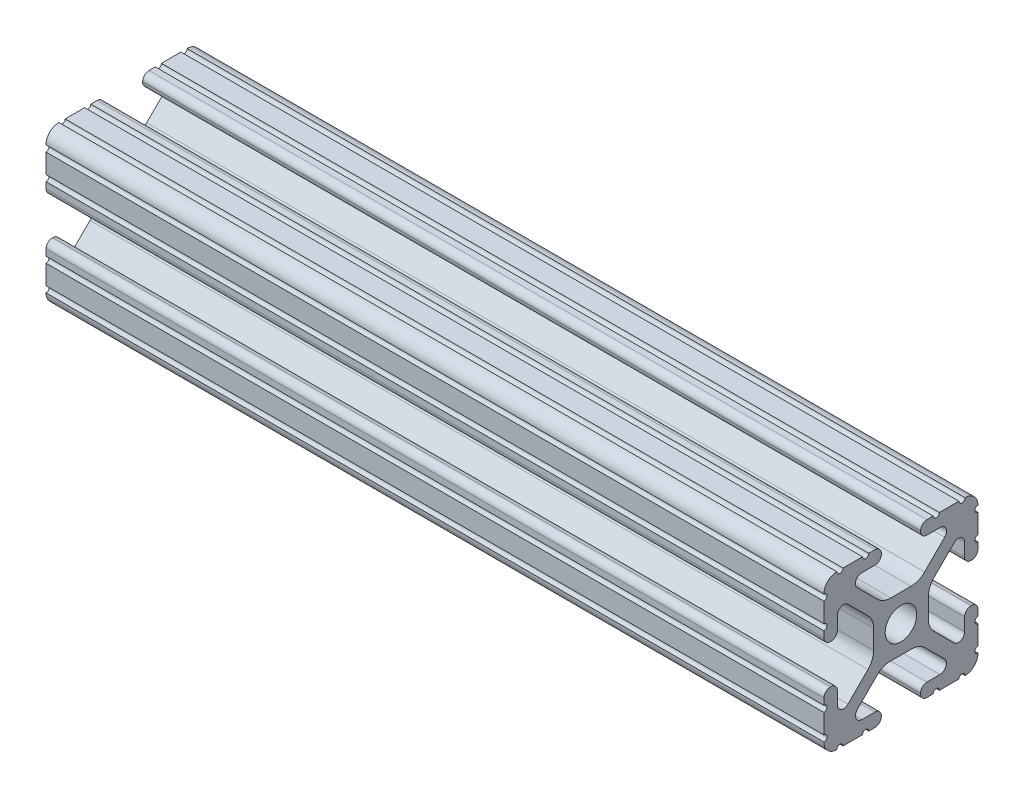
SolidWorks part; units mm, degrees
ref_plane "Front Plane" through (0, 0, 0) normal (0, 0, 1) x (1, 0, 0)
ref_plane "Top Plane" through (0, 0, 0) normal (0, 1, 0) x (1, 0, 0)
ref_plane "Right Plane" through (0, 0, 0) normal (1, 0, 0) x (0, 0, -1)
sketch "Sketch1" plane through (0, 0, 0) normal (0, 1, 0) x (1, 0, 0)
  line L0 (0, 0) -> (-128.27, 0)
  dimension "D1" = 128.27
other "10 1010 PROFILE(1)"
ref_plane "Plane1" through (0, 0, 0) normal (-1, 0, 0) x (0, 0, 1)
sketch "Sketch11" plane through (0, 0, 0) normal (-1, 0, 0) x (0, 0, 1)
  line L1 (12.7, 12.7) -> (-12.7, 12.7) construction
  line L2 (12.7, 12.7) -> (12.7, -12.7) construction
  line L3 (12.7, -12.7) -> (-12.7, -12.7) construction
  line L4 (-12.7, 12.7) -> (-12.7, -12.7) construction
  line L5 (12.7, 12.7) -> (-12.7, -12.7) construction
  line L6 (12.7, -12.7) -> (-12.7, 12.7) construction
  line L88 (-1.7093, -4.4958) -> (1.7093, -4.4958)
  line L89 (3.9523, -5.4237) -> (7.1797, -8.6452)
  line L90 (6.4164, -10.4902) -> (4.2875, -10.4902)
  line L91 (3.2385, -11.5392) -> (3.2385, -11.651)
  line L92 (4.2875, -12.7) -> (5.3171, -12.7)
  line L93 (6.3331, -12.7) -> (9.5504, -12.7)
  line L94 (12.7, -9.5504) -> (12.7, -6.3331)
  line L95 (12.7, -5.3171) -> (12.7, -4.2875)
  line L96 (11.651, -3.2385) -> (11.5392, -3.2385)
  line L97 (10.4902, -4.2875) -> (10.4902, -6.4021)
  line L98 (8.737, -7.1292) -> (5.4405, -3.8388)
  line L99 (4.5085, -1.5917) -> (4.5085, 1.5917)
  line L100 (5.4405, 3.8388) -> (8.737, 7.1292)
  line L101 (10.4902, 6.4021) -> (10.4902, 4.2875)
  line L102 (11.5392, 3.2385) -> (11.651, 3.2385)
  line L103 (12.7, 4.2875) -> (12.7, 5.3171)
  line L104 (12.7, 6.3331) -> (12.7, 9.5504)
  line L105 (9.5504, 12.7) -> (6.3331, 12.7)
  line L106 (5.3171, 12.7) -> (4.2875, 12.7)
  line L107 (3.2384, 11.651) -> (3.2384, 11.5392)
  line L108 (4.2875, 10.4902) -> (6.4768, 10.4902)
  line L109 (7.2072, 8.7245) -> (3.9003, 5.4237)
  line L110 (1.6573, 4.4958) -> (-1.6573, 4.4958)
  line L111 (-3.9003, 5.4237) -> (-7.2072, 8.7245)
  line L112 (-6.4768, 10.4902) -> (-4.2875, 10.4902)
  line L113 (-3.2384, 11.5392) -> (-3.2384, 11.651)
  line L114 (-4.2875, 12.7) -> (-5.3171, 12.7)
  line L115 (-6.3331, 12.7) -> (-9.5504, 12.7)
  line L116 (-12.7, 9.5504) -> (-12.7, 6.3331)
  line L117 (-12.7, 5.3171) -> (-12.7, 4.2875)
  line L118 (-11.651, 3.2385) -> (-11.5392, 3.2385)
  line L119 (-10.4902, 4.2875) -> (-10.4902, 6.4021)
  line L120 (-8.737, 7.1292) -> (-5.4405, 3.8388)
  line L121 (-4.5085, 1.5917) -> (-4.5085, -1.5917)
  line L122 (-5.4405, -3.8388) -> (-8.737, -7.1292)
  line L123 (-10.4902, -6.4021) -> (-10.4902, -4.2875)
  line L124 (-11.5392, -3.2385) -> (-11.651, -3.2385)
  line L125 (-12.7, -4.2875) -> (-12.7, -5.3171)
  line L126 (-12.7, -6.3331) -> (-12.7, -9.5504)
  line L127 (-9.5504, -12.7) -> (-6.3331, -12.7)
  line L128 (-5.3171, -12.7) -> (-4.2875, -12.7)
  line L129 (-3.2385, -11.651) -> (-3.2385, -11.5392)
  line L130 (-4.2875, -10.4902) -> (-6.4164, -10.4902)
  line L131 (-7.1797, -8.6452) -> (-3.9523, -5.4237)
  circle A1 centre (0, 0) radius 2.6035
  arc A104 (-1.7093, -4.4958) -> (-3.9523, -5.4237) centre (-1.7093, -7.6708) ccw
  arc A105 (3.9523, -5.4237) -> (1.7093, -4.4958) centre (1.7093, -7.6708) ccw
  arc A106 (6.4164, -10.4902) -> (7.1797, -8.6452) centre (6.4164, -9.4098) ccw
  arc A107 (4.2875, -10.4902) -> (3.2385, -11.5392) centre (4.2875, -11.5392) ccw
  arc A108 (3.2385, -11.651) -> (4.2875, -12.7) centre (4.2875, -11.651) ccw
  arc A109 (6.3331, -12.7) -> (5.3171, -12.7) centre (5.8251, -12.7) ccw
  arc A110 (10.5664, -12.6998) -> (9.5504, -12.7) centre (10.0584, -12.7) ccw
  arc A111 (10.5664, -12.6998) -> (12.6998, -10.5664) centre (10.5918, -10.5918) ccw
  arc A112 (12.7, -9.5504) -> (12.6998, -10.5664) centre (12.7, -10.0584) ccw
  arc A113 (12.7, -5.3171) -> (12.7, -6.3331) centre (12.7, -5.8251) ccw
  arc A114 (12.7, -4.2875) -> (11.651, -3.2385) centre (11.651, -4.2875) ccw
  arc A115 (11.5392, -3.2385) -> (10.4902, -4.2875) centre (11.5392, -4.2875) ccw
  arc A116 (8.737, -7.1292) -> (10.4902, -6.4021) centre (9.4628, -6.4021) ccw
  arc A117 (4.5085, -1.5917) -> (5.4405, -3.8388) centre (7.6835, -1.5917) ccw
  arc A118 (5.4405, 3.8388) -> (4.5085, 1.5917) centre (7.6835, 1.5917) ccw
  arc A119 (10.4902, 6.4021) -> (8.737, 7.1292) centre (9.4628, 6.4021) ccw
  arc A120 (10.4902, 4.2875) -> (11.5392, 3.2385) centre (11.5392, 4.2875) ccw
  arc A121 (11.651, 3.2385) -> (12.7, 4.2875) centre (11.651, 4.2875) ccw
  arc A122 (12.7, 6.3331) -> (12.7, 5.3171) centre (12.7, 5.8251) ccw
  arc A123 (12.6998, 10.5664) -> (12.7, 9.5504) centre (12.7, 10.0584) ccw
  arc A124 (12.6998, 10.5664) -> (10.5664, 12.6998) centre (10.5918, 10.5918) ccw
  arc A125 (9.5504, 12.7) -> (10.5664, 12.6998) centre (10.0584, 12.7) ccw
  arc A126 (5.3171, 12.7) -> (6.3331, 12.7) centre (5.8251, 12.7) ccw
  arc A127 (4.2875, 12.7) -> (3.2384, 11.651) centre (4.2875, 11.651) ccw
  arc A128 (3.2384, 11.5392) -> (4.2875, 10.4902) centre (4.2875, 11.5392) ccw
  arc A129 (7.2072, 8.7245) -> (6.4768, 10.4902) centre (6.4768, 9.4563) ccw
  arc A130 (1.6573, 4.4958) -> (3.9003, 5.4237) centre (1.6573, 7.6708) ccw
  arc A131 (-3.9003, 5.4237) -> (-1.6573, 4.4958) centre (-1.6573, 7.6708) ccw
  arc A132 (-6.4768, 10.4902) -> (-7.2072, 8.7245) centre (-6.4768, 9.4563) ccw
  arc A133 (-4.2875, 10.4902) -> (-3.2384, 11.5392) centre (-4.2875, 11.5392) ccw
  arc A134 (-3.2384, 11.651) -> (-4.2875, 12.7) centre (-4.2875, 11.651) ccw
  arc A135 (-6.3331, 12.7) -> (-5.3171, 12.7) centre (-5.8251, 12.7) ccw
  arc A136 (-10.5664, 12.6998) -> (-9.5504, 12.7) centre (-10.0584, 12.7) ccw
  arc A137 (-10.5664, 12.6998) -> (-12.6998, 10.5664) centre (-10.5918, 10.5918) ccw
  arc A138 (-12.7, 9.5504) -> (-12.6998, 10.5664) centre (-12.7, 10.0584) ccw
  arc A139 (-12.7, 5.3171) -> (-12.7, 6.3331) centre (-12.7, 5.8251) ccw
  arc A140 (-12.7, 4.2875) -> (-11.651, 3.2385) centre (-11.651, 4.2875) ccw
  arc A141 (-11.5392, 3.2385) -> (-10.4902, 4.2875) centre (-11.5392, 4.2875) ccw
  arc A142 (-8.737, 7.1292) -> (-10.4902, 6.4021) centre (-9.4628, 6.4021) ccw
  arc A143 (-4.5085, 1.5917) -> (-5.4405, 3.8388) centre (-7.6835, 1.5917) ccw
  arc A144 (-5.4405, -3.8388) -> (-4.5085, -1.5917) centre (-7.6835, -1.5917) ccw
  arc A145 (-10.4902, -6.4021) -> (-8.737, -7.1292) centre (-9.4628, -6.4021) ccw
  arc A146 (-10.4902, -4.2875) -> (-11.5392, -3.2385) centre (-11.5392, -4.2875) ccw
  arc A147 (-11.651, -3.2385) -> (-12.7, -4.2875) centre (-11.651, -4.2875) ccw
  arc A148 (-12.7, -6.3331) -> (-12.7, -5.3171) centre (-12.7, -5.8251) ccw
  arc A149 (-12.6998, -10.5664) -> (-12.7, -9.5504) centre (-12.7, -10.0584) ccw
  arc A150 (-12.6998, -10.5664) -> (-10.5664, -12.6998) centre (-10.5918, -10.5918) ccw
  arc A151 (-9.5504, -12.7) -> (-10.5664, -12.6998) centre (-10.0584, -12.7) ccw
  arc A152 (-5.3171, -12.7) -> (-6.3331, -12.7) centre (-5.8251, -12.7) ccw
  arc A153 (-4.2875, -12.7) -> (-3.2385, -11.651) centre (-4.2875, -11.651) ccw
  arc A154 (-3.2385, -11.5392) -> (-4.2875, -10.4902) centre (-4.2875, -11.5392) ccw
  arc A155 (-7.1797, -8.6452) -> (-6.4164, -10.4902) centre (-6.4164, -9.4098) ccw
  point P3 (0, 0)
  point P21 (-12.7, 0)
  point P22 (0, 12.7)
  point P25 (12.7, 0)
  point P28 (0, -12.7)
  point P30 (-12.7, -12.7)
  point P33 (12.7, -12.7)
  point P37 (12.7, 12.7)
  point P40 (-12.7, 12.7)
  point P43 (0, 0)
  dimension "D1" = 25.4
